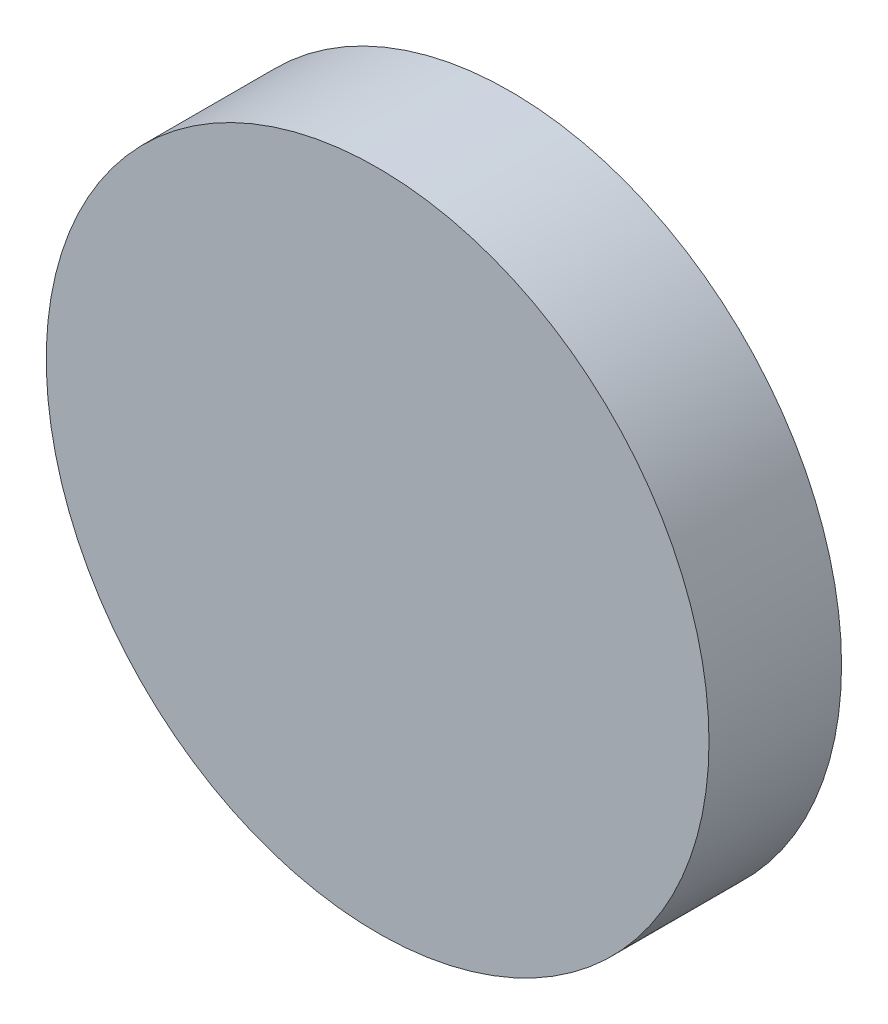
SolidWorks part; units mm, degrees
ref_plane "Alzado" through (0, 0, 0) normal (0, 0, 1) x (1, 0, 0)
ref_plane "Planta" through (0, 0, 0) normal (0, 1, 0) x (1, 0, 0)
ref_plane "Vista lateral" through (0, 0, 0) normal (1, 0, 0) x (0, 0, -1)
sketch "Croquis1" plane through (0, 0, 0) normal (0, 0, 1) x (1, 0, 0)
  circle A0 centre (0, 0) radius 5
  dimension "D1" = 10
extrude "Saliente-Extruir1" add sketch "Croquis1" along normal blind 2
sketch "Croquis2" plane through (0, 0, 0) normal (0, 0, -1) x (-1, 0, 0)
  circle A0 centre (0, 0) radius 2
  dimension "D1" = 4
extrude "Cortar-Extruir1" cut sketch "Croquis2" against normal blind 0.5
